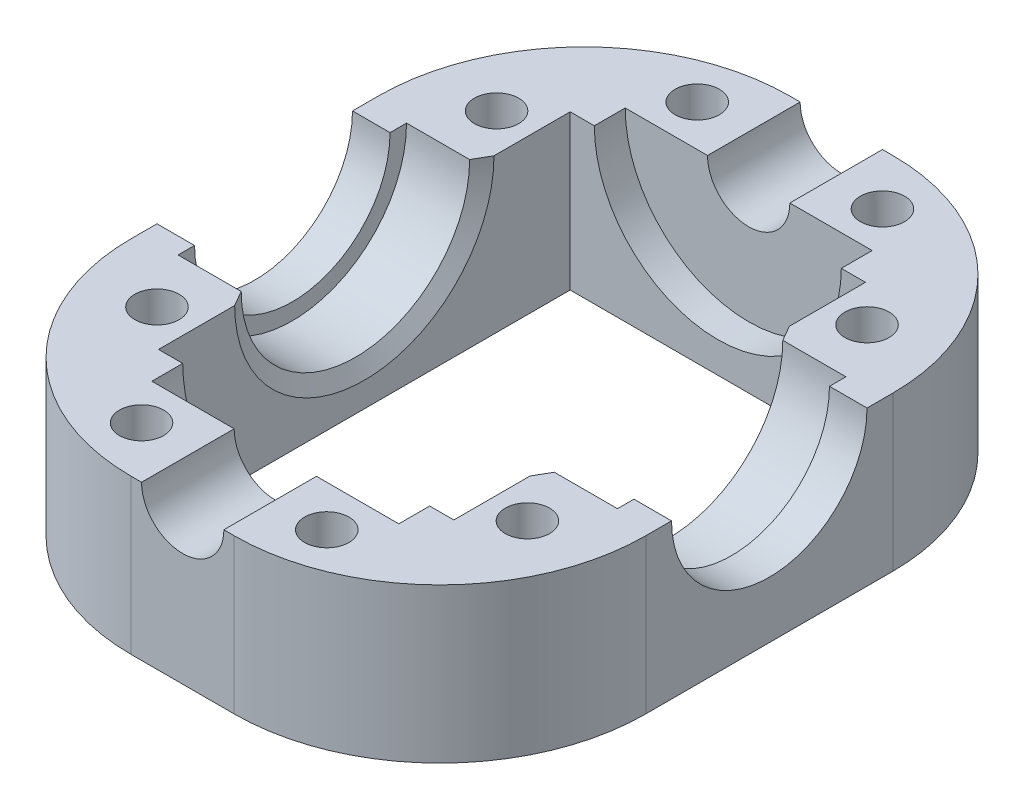
SolidWorks part; units mm, degrees
ref_plane "Спереди" through (0, 0, 0) normal (0, 0, 1) x (1, 0, 0)
ref_plane "Сверху" through (0, 0, 0) normal (0, 1, 0) x (1, 0, 0)
ref_plane "Справа" through (0, 0, 0) normal (1, 0, 0) x (0, 0, -1)
sketch "Sketch1" plane through (0, 0, 0) normal (0, 1, 0) x (1, 0, 0)
  line L1 (25, -32) -> (-25, -32)
  line L2 (25, -32) -> (25, 32)
  line L3 (25, 32) -> (-25, 32)
  line L4 (-25, -32) -> (-25, 32)
  line L5 (25, -32) -> (-25, 32) construction
  line L6 (25, 32) -> (-25, -32) construction
  line L7 (14.35, -20) -> (-14.35, -20)
  line L8 (14.35, -20) -> (14.35, 20)
  line L9 (14.35, 20) -> (-14.35, 20)
  line L10 (-14.35, -20) -> (-14.35, 20)
  line L11 (14.35, -20) -> (-14.35, 20) construction
  line L12 (14.35, 20) -> (-14.35, -20) construction
  point P0 (0, 0)
  point P6 (0, 0)
  dimension "D1" = 50
  dimension "D2" = 64
  dimension "D3" = 40
  dimension "D4" = 28.7
extrude "Boss-Extrude1" add sketch "Sketch1" along normal blind 15
sketch "Sketch3" plane through (0, 15, 0) normal (0, 1, 0) x (1, 0, 0)
  line L0 (-14.35, 0) -> (-25, 0) construction
  line L1 (-14.35, 20) -> (-14.35, -20) construction
  line L2 (-25, 32) -> (-25, -32) construction
  line L3 (14.35, 0) -> (25, 0) construction
  line L4 (14.35, -20) -> (14.35, 20) construction
  line L5 (25, -32) -> (25, 32) construction
  line L10 (14.35, -11.1) -> (21.35, -11.1)
  line L11 (14.35, -11.1) -> (14.35, 0)
  line L12 (14.35, 0) -> (21.35, 0)
  line L13 (21.35, -11.1) -> (21.35, 0)
  line L14 (14.35, -11.1) -> (21.35, 0) construction
  line L15 (14.35, 0) -> (21.35, -11.1) construction
  line L16 (-21.35, -11.1) -> (-14.35, -11.1)
  line L17 (-21.35, -11.1) -> (-21.35, 0)
  line L18 (-21.35, 0) -> (-14.35, 0)
  line L19 (-14.35, -11.1) -> (-14.35, 0)
  line L20 (-21.35, -11.1) -> (-14.35, 0) construction
  line L21 (-21.35, 0) -> (-14.35, -11.1) construction
  point P18 (17.85, -5.55)
  point P23 (-17.85, -5.55)
  dimension "D1" = 7
  dimension "D2" = 11.1
revolve "Cut-Revolve1" cut sketch "Sketch3" angle 360 about L12
sketch "Sketch4" plane through (25, 0, 0) normal (1, 0, 0) x (0, 0, -1)
  line L0 (-32, 15) -> (32, 15) construction
  circle A0 centre (0, 15) radius 9.5
  dimension "D1" = 19
extrude "Cut-Extrude2" cut sketch "Sketch4" against normal through all
sketch "Sketch5" plane through (0, 0, 32) normal (0, 0, 1) x (1, 0, 0)
  line L0 (-25, 15) -> (25, 15) construction
  circle A0 centre (0, 15) radius 4
  dimension "D1" = 8
extrude "Cut-Extrude3" cut sketch "Sketch5" against normal through all
sketch "Sketch8" plane through (0, 15, 0) normal (0, 1, 0) x (1, 0, 0)
  line L1 (-18, -16.5) -> (18, -16.5) construction
  line L2 (-18, -16.5) -> (-18, 16.5) construction
  line L3 (-18, 16.5) -> (18, 16.5) construction
  line L4 (18, -16.5) -> (18, 16.5) construction
  line L5 (-18, -16.5) -> (18, 16.5) construction
  line L6 (-18, 16.5) -> (18, -16.5) construction
  line L7 (-9, 27) -> (9, 27) construction
  line L8 (-9, 27) -> (-9, -27) construction
  line L9 (-9, -27) -> (9, -27) construction
  line L10 (9, 27) -> (9, -27) construction
  line L11 (-9, 27) -> (9, -27) construction
  line L12 (-9, -27) -> (9, 27) construction
  circle A0 centre (18, 16.5) radius 2.15
  circle A1 centre (18, -16.5) radius 2.15
  circle A2 centre (-18, -16.5) radius 2.15
  circle A3 centre (-18, 16.5) radius 2.15
  circle A4 centre (9, -27) radius 2.15
  circle A5 centre (-9, -27) radius 2.15
  circle A6 centre (-9, 27) radius 2.15
  circle A7 centre (9, 27) radius 2.15
  point P0 (0, 0)
  point P10 (0, 0)
  dimension "D3" = 4.3
  dimension "D1" = 33
  dimension "D2" = 36
  dimension "D4" = 18
  dimension "D5" = 54
extrude "Cut-Extrude6" cut sketch "Sketch8" against normal through all
fillet "Fillet1" radius 20 4 edges at (-25, 7.5, 32) (-25, 7.5, -32) (25, 7.5, -32) (25, 7.5, 32)
chamfer "Chamfer1" distance 1.5 angle 30 2 edges at (-14.35, 3.9, 0) (14.35, 3.9, 0)
sketch "Sketch9" plane through (0, 15, 0) normal (0, 1, 0) x (1, 0, 0)
  line L0 (0, 29.8714) -> (0, -31.0419) construction
  line L1 (-4, 20) -> (-14.35, 20) construction
  line L2 (-12, -23) -> (0, -23)
  line L3 (-12, -23) -> (-12, -20)
  line L4 (-12, -20) -> (0, -20)
  line L5 (0, -23) -> (0, -20)
  line L6 (-12, -23) -> (0, -20) construction
  line L7 (-12, -20) -> (0, -23) construction
  line L8 (-12, 20) -> (0, 20)
  line L9 (-12, 20) -> (-12, 23)
  line L10 (-12, 23) -> (0, 23)
  line L11 (0, 20) -> (0, 23)
  line L12 (-12, 20) -> (0, 23) construction
  line L13 (-12, 23) -> (0, 20) construction
  line L14 (-14.35, -20) -> (-4, -20) construction
  point P3 (-6, -21.5)
  point P8 (-6, 21.5)
  dimension "D1" = 3
  dimension "D2" = 12
revolve "Cut-Revolve2" cut sketch "Sketch9" angle 360 about L0
